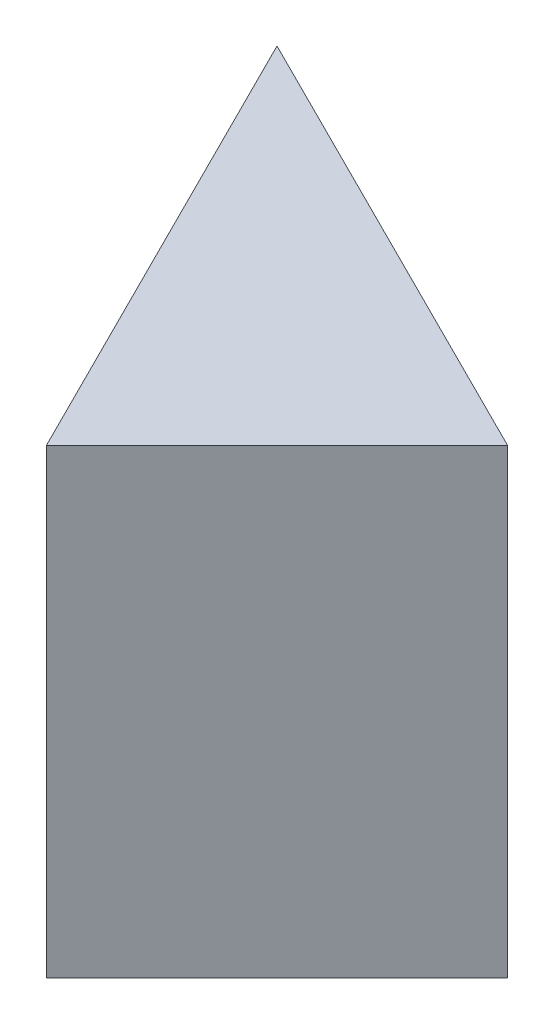
SolidWorks part; units mm, degrees
ref_plane "Front Plane" through (0, 0, 0) normal (0, 0, 1) x (1, 0, 0)
ref_plane "Top Plane" through (0, 0, 0) normal (0, 1, 0) x (1, 0, 0)
ref_plane "Right Plane" through (0, 0, 0) normal (1, 0, 0) x (0, 0, -1)
sketch "Sketch1" plane through (0, 0, 0) normal (0, 0, 1) x (1, 0, 0)
  line L1 (0, 0) -> (20, 0)
  line L2 (0, 0) -> (0, 20)
  line L3 (0, 20) -> (20, 20)
  line L4 (20, 0) -> (20, 20)
  dimension "D1" = 20
  dimension "D2" = 20
extrude "Boss-Extrude1" add sketch "Sketch1" along normal blind 20
sketch "Sketch2" plane through (0, 20, 0) normal (0, 1, 0) x (1, 0, 0)
  line L0 (0, 0) -> (20, 0)
  line L1 (20, 0) -> (20, -10)
  line L2 (20, -20) -> (20, 0) construction
  line L3 (20, -10) -> (0, 0)
extrude "Cut-Extrude1" cut sketch "Sketch2" against normal blind 20
sketch "Sketch3" plane through (0, 20, 0) normal (0, 1, 0) x (1, 0, 0)
  line L0 (0, 0) -> (0, -20)
  line L1 (0, -20) -> (10, -20)
  line L2 (20, -20) -> (0, -20) construction
  line L3 (10, -20) -> (0, 0)
extrude "Cut-Extrude2" cut sketch "Sketch3" against normal blind 20
sketch "Sketch4" plane through (0, 20, 0) normal (0, 1, 0) x (1, 0, 0)
  line L0 (20, -20) -> (20, -10)
  line L1 (20, -10) -> (10, -20)
  line L2 (10, -20) -> (20, -20)
extrude "Cut-Extrude3" cut sketch "Sketch4" against normal blind 20
